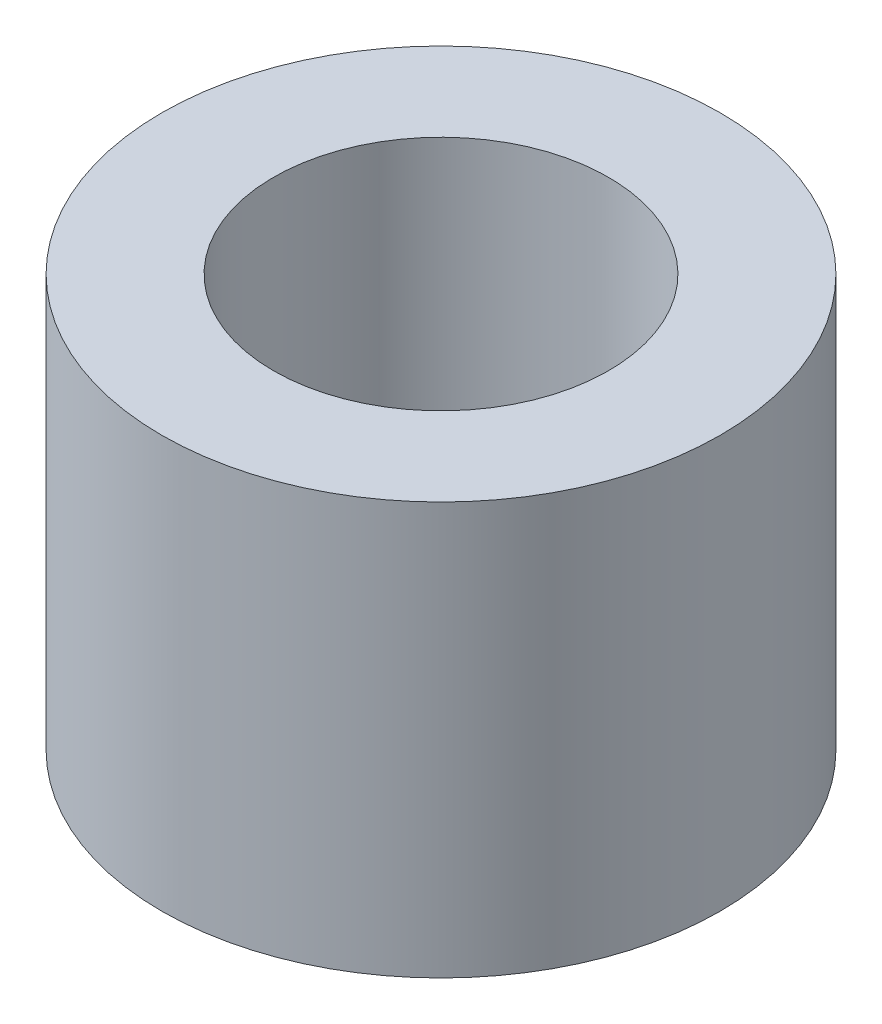
SolidWorks part; units mm, degrees
ref_plane "Front Plane" through (0, 0, 0) normal (0, 0, 1) x (1, 0, 0)
ref_plane "Top Plane" through (0, 0, 0) normal (0, 1, 0) x (1, 0, 0)
ref_plane "Right Plane" through (0, 0, 0) normal (1, 0, 0) x (0, 0, -1)
sketch "Sketch1" plane through (0, 0, 0) normal (0, 1, 0) x (1, 0, 0)
  circle A0 centre (0, 0) radius 5
extrude "Boss-Extrude1" add sketch "Sketch1" along normal blind 7.38
sketch "Sketch2" plane through (0, 7.38, 0) normal (0, 1, 0) x (1, 0, 0)
  circle A0 centre (0, 0) radius 3
extrude "Cut-Extrude1" cut sketch "Sketch2" against normal blind 7.38
